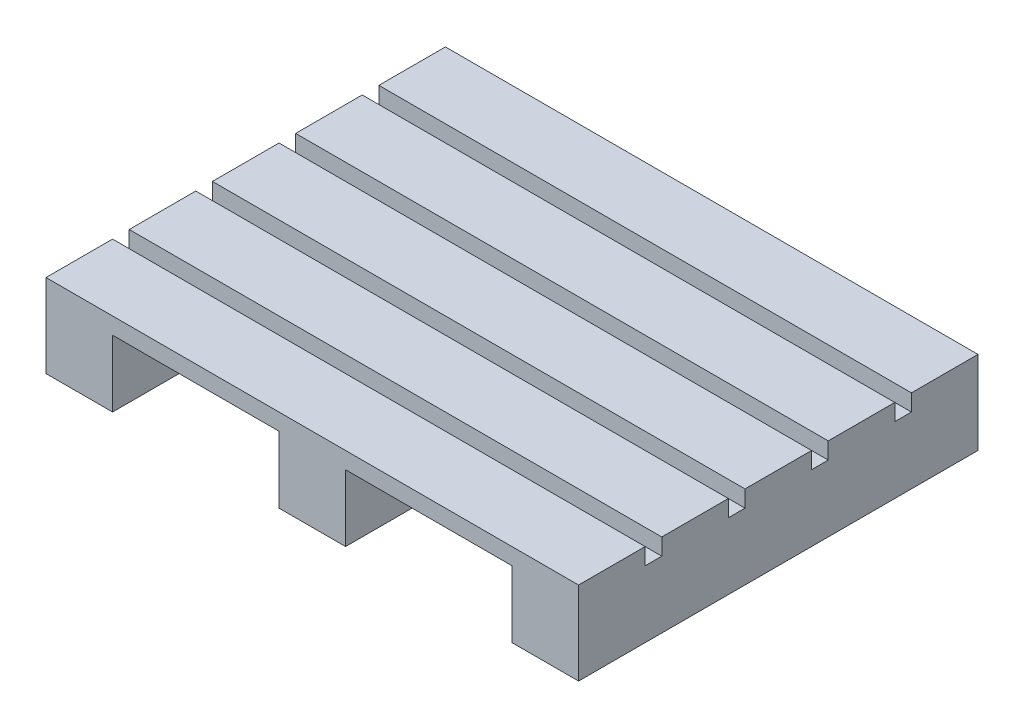
SolidWorks part; units mm, degrees
material "ABS"
ref_plane "Alzado" through (0, 0, 0) normal (0, 0, 1) x (1, 0, 0)
ref_plane "Planta" through (0, 0, 0) normal (0, 1, 0) x (1, 0, 0)
ref_plane "Vista lateral" through (0, 0, 0) normal (1, 0, 0) x (0, 0, -1)
sketch "Croquis1" plane through (0, 0, 0) normal (0, 1, 0) x (1, 0, 0)
  line L1 (-56.8494, 21.9312) -> (-46.8494, 21.9312)
  line L2 (-56.8494, 21.9312) -> (-56.8494, -38.0688)
  line L3 (-56.8494, -38.0688) -> (-46.8494, -38.0688)
  line L4 (-46.8494, 21.9312) -> (-46.8494, -38.0688)
  line L5 (-21.8494, 21.9312) -> (-11.8494, 21.9312)
  line L6 (-21.8494, 21.9312) -> (-21.8494, -38.0688)
  line L7 (-21.8494, -38.0688) -> (-11.8494, -38.0688)
  line L8 (-11.8494, 21.9312) -> (-11.8494, -38.0688)
  line L9 (13.1506, 21.9312) -> (23.1506, 21.9312)
  line L10 (13.1506, 21.9312) -> (13.1506, -38.0688)
  line L11 (13.1506, -38.0688) -> (23.1506, -38.0688)
  line L12 (23.1506, 21.9312) -> (23.1506, -38.0688)
  dimension "D1" = 60
  dimension "D2" = 60
  dimension "D3" = 60
  dimension "D4" = 10
  dimension "D5" = 10
  dimension "D6" = 10
  dimension "D7" = 25
  dimension "D8" = 25
extrude "Saliente-Extruir1" add sketch "Croquis1" along normal blind 10
sketch "Croquis2" plane through (0, 10, 0) normal (0, 1, 0) x (1, 0, 0)
  line L0 (23.1506, -38.0688) -> (23.1506, 21.9312) construction
  line L1 (-56.8494, -38.0688) -> (23.1506, -38.0688)
  line L2 (-56.8494, -38.0688) -> (-56.8494, -28.0688)
  line L3 (-56.8494, -28.0688) -> (23.1506, -28.0688)
  line L4 (23.1506, -38.0688) -> (23.1506, -28.0688)
  line L5 (-56.8494, 21.9312) -> (-56.8494, -38.0688) construction
  line L6 (-56.8494, 21.9312) -> (23.1506, 21.9312)
  line L7 (-56.8494, 21.9312) -> (-56.8494, 11.9312)
  line L8 (-56.8494, 11.9312) -> (23.1506, 11.9312)
  line L9 (23.1506, 21.9312) -> (23.1506, 11.9312)
  line L10 (-56.8494, 9.4312) -> (23.1506, 9.4312)
  line L11 (-56.8494, 9.4312) -> (-56.8494, -0.5688)
  line L12 (-56.8494, -0.5688) -> (23.1506, -0.5688)
  line L13 (23.1506, 9.4312) -> (23.1506, -0.5688)
  line L15 (-56.8494, -25.5688) -> (23.1506, -25.5688)
  line L16 (-56.8494, -25.5688) -> (-56.8494, -15.5688)
  line L17 (-56.8494, -15.5688) -> (23.1506, -15.5688)
  line L18 (23.1506, -25.5688) -> (23.1506, -15.5688)
  line L19 (-56.8494, -3.0688) -> (23.1506, -3.0688)
  line L20 (-56.8494, -3.0688) -> (-56.8494, -13.0688)
  line L21 (-56.8494, -13.0688) -> (23.1506, -13.0688)
  line L22 (23.1506, -3.0688) -> (23.1506, -13.0688)
  dimension "D1" = 10
  dimension "D2" = 10
  dimension "D3" = 2.5
  dimension "D4" = 10
  dimension "D5" = 2.5
  dimension "D6" = 10
  dimension "D7" = 10
  dimension "D8" = 2.5
  dimension "D9" = 2.5
extrude "Saliente-Extruir2" add sketch "Croquis2" along normal blind 2.5
